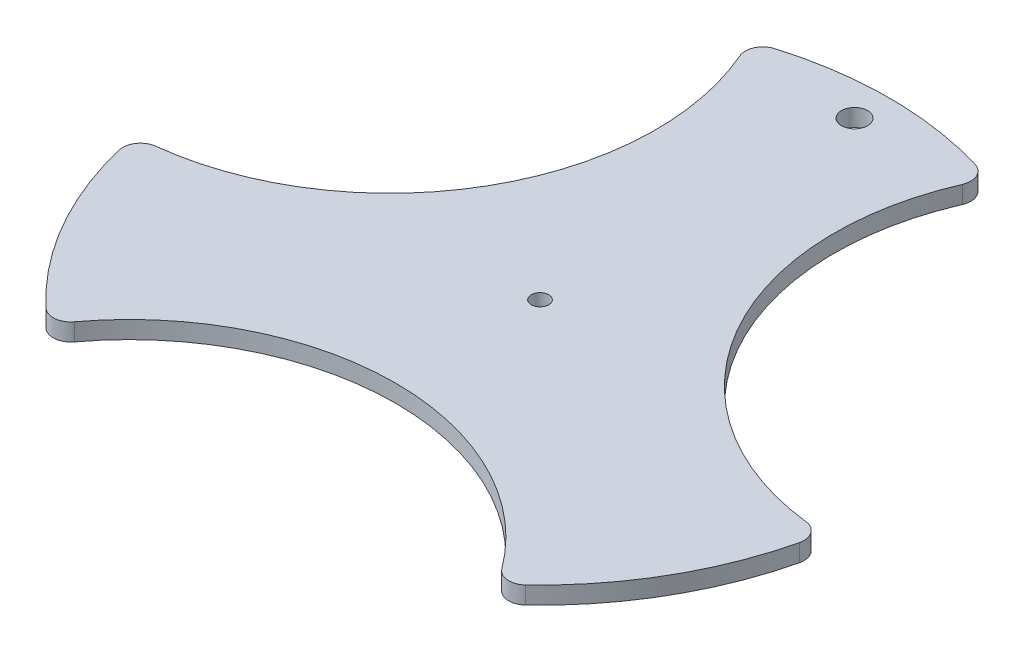
SolidWorks part; units mm, degrees
ref_plane "Front Plane" through (0, 0, 0) normal (0, 0, 1) x (1, 0, 0)
ref_plane "Top Plane" through (0, 0, 0) normal (0, 1, 0) x (1, 0, 0)
ref_plane "Right Plane" through (0, 0, 0) normal (1, 0, 0) x (0, 0, -1)
sketch "Sketch1" plane through (0, 0, 0) normal (0, 1, 0) x (1, 0, 0)
  circle A0 centre (0, 0) radius 40
  dimension "D1" = 80
extrude "Boss-Extrude1" add sketch "Sketch1" along normal blind 2
sketch "Sketch2" plane through (0, 0, 0) normal (0, 1, 0) x (1, 0, 0)
  line L0 (-13.6808, 37.5877) -> (0, 0) construction
  line L1 (0, 0) -> (13.6808, 37.5877) construction
  line L2 (0, -1000) -> (0, 49000) construction
  line L3 (-13.6808, 37.5877) -> (-10.9446, 30.0702)
  line L4 (13.6808, 37.5877) -> (10.9446, 30.0702)
  line L5 (39.3923, -6.9459) -> (31.5138, -5.5567)
  line L6 (25.7115, -30.6418) -> (20.5692, -24.5134)
  line L7 (-25.7115, -30.6418) -> (-20.5692, -24.5134)
  line L8 (-39.3923, -6.9459) -> (-31.5138, -5.5567)
  circle A0 centre (0, 0) radius 40 construction
  arc A1 (-13.6808, 37.5877) -> (13.6808, 37.5877) centre (0, 0) cw
  arc A2 (-10.9446, 30.0702) -> (10.9446, 30.0702) centre (0, 0) cw
  arc A3 (39.3923, -6.9459) -> (25.7115, -30.6418) centre (0, 0) cw
  arc A4 (31.5138, -5.5567) -> (20.5692, -24.5134) centre (0, 0) cw
  arc A5 (-25.7115, -30.6418) -> (-39.3923, -6.9459) centre (0, 0) cw
  arc A6 (-20.5692, -24.5134) -> (-31.5138, -5.5567) centre (0, 0) cw
  point P21 (0, 0)
  dimension "D1" = 20
  dimension "D2" = 20
  dimension "D3" = 8
  dimension "D4" = 3
sketch "Sketch5" plane through (0, 2, 0) normal (0, 1, 0) x (1, 0, 0)
  circle A0 centre (0, 36) radius 1.5
  dimension "D2" = 3
  dimension "D1" = 36
extrude "Cut-Extrude2" cut sketch "Sketch5" against normal through all
sketch "Sketch7" plane through (0, 2, 0) normal (0, 1, 0) x (1, 0, 0)
  circle A0 centre (0, 0) radius 1
  dimension "D1" = 2
extrude "Cut-Extrude4" cut sketch "Sketch7" against normal through all
sketch "Sketch8" plane through (0, 2, 0) normal (0, 1, 0) x (1, 0, 0)
  circle A0 centre (40.6986, 23.4973) radius 30.4713
extrude "Cut-Extrude5" cut sketch "Sketch8" against normal through all
pattern_circular "CirPattern1" count 3 over 360 about axis through (0, 0, 0) along (0, 1, 0) of "Cut-Extrude5"
fillet "Fillet1" radius 2 6 edges at (-39.3923, 1, 6.9459) (-13.6808, 1, -37.5877) (13.6808, 1, -37.5877) (39.3923, 1, 6.9459) (25.7115, 1, 30.6418) (-25.7115, 1, 30.6418)
